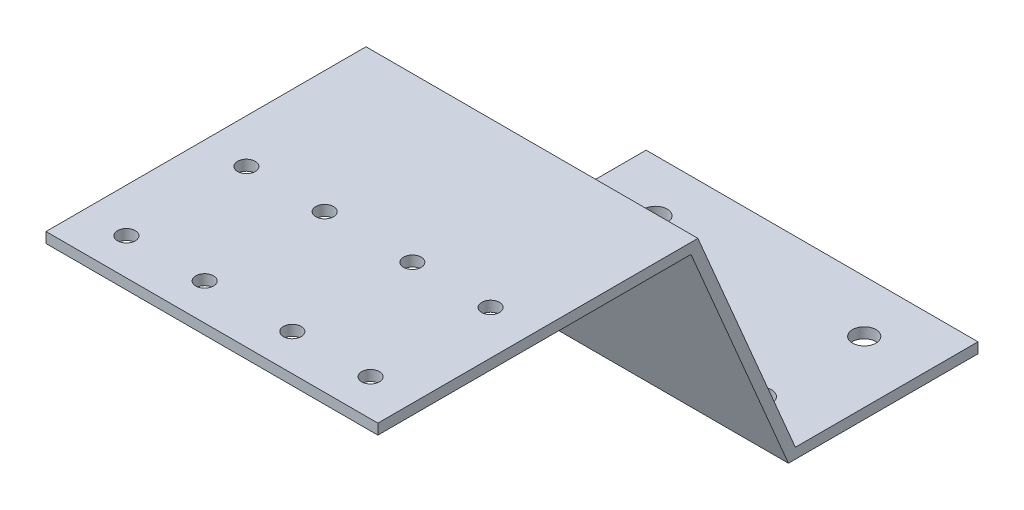
SolidWorks part; units mm, degrees
material "6061 Alloy"
ref_plane "Front Plane" through (0, 0, 0) normal (0, 0, 1) x (1, 0, 0)
ref_plane "Top Plane" through (0, 0, 0) normal (0, 1, 0) x (1, 0, 0)
ref_plane "Right Plane" through (0, 0, 0) normal (1, 0, 0) x (0, 0, -1)
sketch "Sketch2" plane through (0, 0, 0) normal (1, 0, 0) x (0, 0, -1)
  line L0 (0, 0) -> (0, 2)
  line L1 (0, 2) -> (-35, 2)
  line L2 (-35, 2) -> (-53.6762, 46)
  line L3 (-53.6762, 46) -> (-115, 46)
  line L4 (0, 0) -> (-36.3238, 0)
  line L5 (-115, 46) -> (-115, 44)
  line L6 (-36.3238, 0) -> (-55, 44)
  line L7 (-55, 44) -> (-115, 44)
  line L8 (-2, 0) -> (-2, 0) construction
  line L9 (-2, 0) -> (-36.3238, 0) construction
  dimension "D2" = 60
  dimension "D3" = 44
  dimension "D4" = 115
  dimension "D5" = 35
  dimension "D1" = 2
extrude "Sheet Extrude" add sketch "Sketch2" along normal mid plane 63.6
hole_wizard "M3 Clearance Hole1" positions "Sketch5" profile "Sketch6" hole size "M3" standard "ANSI Metric"
sketch "Sketch5" plane through (0, 46, 0) normal (0, 1, 0) x (1, 0, 0)
  line L0 (0, -127.4881) -> (0, -27.1774) construction
  line L2 (31.8, -115) -> (-31.8, -115) construction
  point P0 (-23.4, -108)
  point P2 (-23.4, -85)
  point P4 (-8.4, -85)
  point P6 (-8.4, -108)
  point P16 (23.4, -108)
  point P17 (8.4, -108)
  point P18 (8.4, -85)
  point P19 (23.4, -85)
  dimension "D1" = 23
  dimension "D2" = 15
  dimension "D3" = 8.4
  dimension "D4" = 7
sketch "Sketch6" plane through (-23.4, 46, 108) normal (1, 0, 0) x (0, 0, 1)
  line L0 (0, 0) -> (0, 9.5215)
  line L1 (0, 9.5215) -> (1.7, 8.5)
  line L2 (1.7, 8.5) -> (1.7, 0)
  line L5 (1.7, 0) -> (0, 0)
  line L10 (0, 9.5215) -> (-1.7, 8.5) construction
  line L11 (0, -6.35) -> (0, 107.95) construction
  dimension "Hole Dia." = 3.4
  dimension "Hole Depth" = 8.5
  dimension "Drill Angle" = 118
hole_wizard "M4 Clearance Hole1" positions "Sketch7" profile "Sketch8" hole size "M4" standard "ANSI Metric"
sketch "Sketch7" plane through (0, 2, 0) normal (0, 1, 0) x (1, 0, 0)
  line L0 (0, 6.97) -> (0, -46.1018) construction
  line L2 (-31.8, -20) -> (52.4815, -20) construction
  line L4 (31.8, 0) -> (-31.8, 0) construction
  point P0 (-20, -30)
  point P2 (20, -30)
  point P4 (20, -10)
  point P6 (-20, -10)
  dimension "D1" = 10
  dimension "D2" = 10
  dimension "D3" = 20
  dimension "D4" = 20
  dimension "D5" = 20
sketch "Sketch8" plane through (-20, 2, 30) normal (1, 0, 0) x (0, 0, 1)
  line L0 (0, 0) -> (0, 9.8519)
  line L1 (0, 9.8519) -> (2.25, 8.5)
  line L2 (2.25, 8.5) -> (2.25, 0)
  line L5 (2.25, 0) -> (0, 0)
  line L10 (0, 9.8519) -> (-2.25, 8.5) construction
  line L11 (0, -6.35) -> (0, 107.95) construction
  dimension "Hole Dia." = 4.5
  dimension "Hole Depth" = 8.5
  dimension "Drill Angle" = 118
